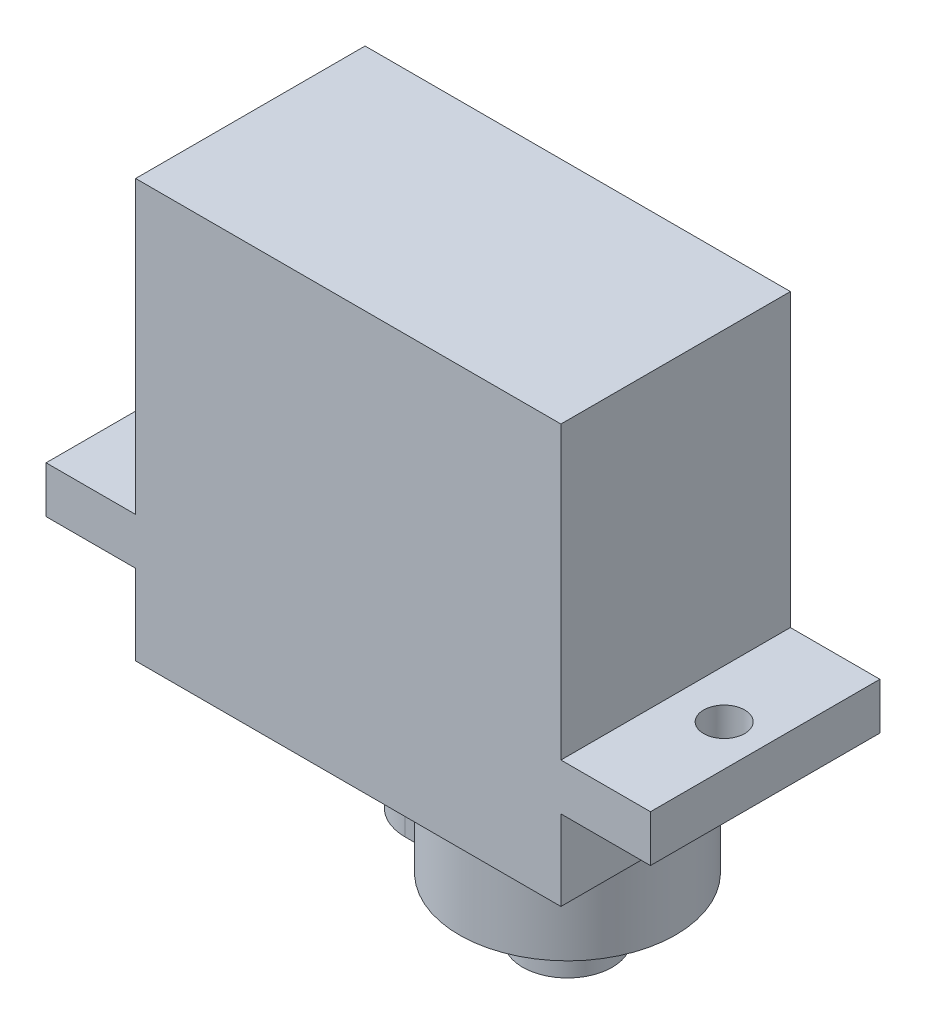
SolidWorks part; units mm, degrees
ref_plane "前基準面" through (0, 0, 0) normal (0, 0, 1) x (1, 0, 0)
ref_plane "上基準面" through (0, 0, 0) normal (0, 1, 0) x (1, 0, 0)
ref_plane "右基準面" through (0, 0, 0) normal (1, 0, 0) x (0, 0, -1)
sketch "Sketch1" plane through (0, 0, 0) normal (0, 0, 1) x (1, 0, 0)
  line L0 (-16.2, 0) -> (-11.4, 0)
  line L1 (16.2, 0) -> (16.2, 2.5)
  line L2 (16.2, 2.5) -> (11.4, 2.5)
  line L3 (11.4, 2.5) -> (11.4, 18.1)
  line L4 (11.4, 18.1) -> (-11.4, 18.1)
  line L5 (-11.4, 18.1) -> (-11.4, 2.5)
  line L6 (-11.4, 2.5) -> (-16.2, 2.5)
  line L7 (-16.2, 2.5) -> (-16.2, 0)
  line L8 (0, 18.1) -> (0, 0) construction
  line L9 (-11.4, 0) -> (-11.4, -4.3)
  line L10 (-11.4, -4.3) -> (11.4, -4.3)
  line L11 (11.4, -4.3) -> (11.4, 0)
  line L12 (11.4, 0) -> (16.2, 0)
  line L13 (-11.4, 0) -> (11.4, 0) construction
  dimension "D1" = 2.5
  dimension "D2" = 15.6
  dimension "D3" = 32.4
  dimension "D4" = 2.5
  dimension "D5" = 22.8
  dimension "D6" = 4.3
  dimension "D7" = 4.8
extrude "Boss-Extrude1" add sketch "Sketch1" along normal blind 12.3
sketch "Sketch2" plane through (0, -4.3, 0) normal (0, -1, 0) x (1, 0, 0)
  line L0 (16.2, 6.15) -> (5.6, 6.15) construction
  line L1 (16.2, 12.3) -> (16.2, 0) construction
  line L2 (-0.4, 8.85) -> (0.4668, 8.85)
  line L3 (5.6, 6.15) -> (-0.4, 6.15) construction
  line L4 (-0.4, 3.45) -> (0.4668, 3.45)
  line L5 (11.4, 12.3) -> (11.4, 0) construction
  arc A0 (0.4668, 3.45) -> (0.4668, 8.85) centre (5.6, 6.15) ccw
  arc A1 (-0.4, 8.85) -> (-0.4, 3.45) centre (-0.4, 6.15) ccw
  dimension "D1" = 11.6
  dimension "D3" = 5.4
  dimension "D4" = 6
extrude "Boss-Extrude2" add sketch "Sketch2" along normal blind 4.4
sketch "Sketch3" plane through (0, 2.5, 0) normal (0, 1, 0) x (1, 0, 0)
  line L0 (-16.2, -6.15) -> (-14, -6.15) construction
  line L1 (-16.2, -12.3) -> (-16.2, 0) construction
  line L2 (16.2, -6.15) -> (14, -6.15) construction
  line L3 (16.2, -12.3) -> (16.2, 0) construction
  circle A0 centre (-14, -6.15) radius 1.1
  circle A1 centre (14, -6.15) radius 1.1
  dimension "D1" = 2.2
  dimension "D2" = 2.2
  dimension "D5" = 28
  dimension "D3" = 2.2
  dimension "D4" = 2.2
extrude "Cut-Extrude1" cut sketch "Sketch3" against normal blind 8
sketch "草圖1" plane through (0, -8.7, 0) normal (0, -1, 0) x (-1, 0, 0)
  circle A0 centre (-5.6, -6.15) radius 2.4
  dimension "D1" = 4.8
extrude "填料-伸長1" add sketch "草圖1" along normal blind 3.2 separate body
